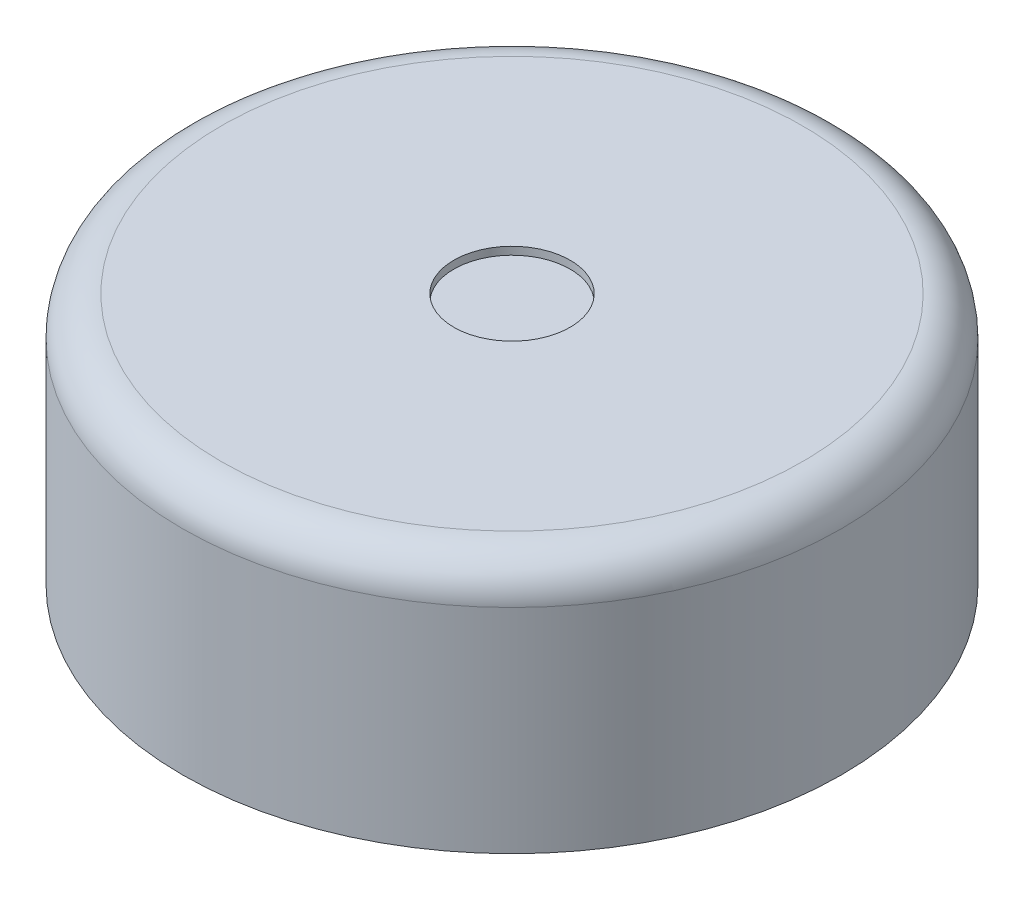
SolidWorks part; units mm, degrees
material "ABS"
ref_plane "Front Plane" through (0, 0, 0) normal (0, 0, 1) x (1, 0, 0)
ref_plane "Top Plane" through (0, 0, 0) normal (0, 1, 0) x (1, 0, 0)
ref_plane "Right Plane" through (0, 0, 0) normal (1, 0, 0) x (0, 0, -1)
sketch "Sketch1" plane through (0, 0, 0) normal (0, 1, 0) x (1, 0, 0)
  circle A0 centre (0, 0) radius 8.5
  dimension "D1" = 17
extrude "Boss-Extrude1" add sketch "Sketch1" along normal blind 7.8
sketch "Sketch2" plane through (0, 7.8, 0) normal (0, 1, 0) x (1, 0, 0)
  circle A1 centre (0, 0) radius 8.5
  circle A2 centre (0, 0) radius 8.5
  circle A3 centre (0, 0) radius 1.5
  circle A4 centre (0, 0) radius 7.8
  circle A5 centre (0, 0) radius 7.8
  circle M3 centre (0, 0) radius 8.5
  dimension "D3" = 3
  dimension "D1" = 0
  dimension "D2" = 0.7
extrude "Cut-Extrude1" cut sketch "Sketch2" against normal blind 1.5 contours A3 | A5 M3
sketch "Sketch3" plane through (0, 0, 0) normal (0, -1, 0) x (1, 0, 0)
  line L0 (-5, 5) -> (5, -5) construction
  circle A0 centre (-5, 5) radius 0.5
  circle A1 centre (5, -5) radius 0.5
  point P4 (0, 0)
  dimension "D1" = 1
  dimension "D2" = 10
  dimension "D3" = 10
extrude "Boss-Extrude2" add sketch "Sketch3" along normal blind 2
chamfer "Chamfer1" distance 0.5 distance2 0.1 2 edges at (-5, -2, 4.5) (5, -2, -5.5)
fillet "Fillet1" radius 1 2 edges at (-5, -1.5, 4.5) (5, -1.5, -5.5)
sketch "Sketch4" plane through (0, 7.8, 0) normal (0, 1, 0) x (1, 0, 0)
  circle A1 centre (0, 0) radius 7.8
  circle A2 centre (0, 0) radius 7.8
  dimension "D1" = 0
extrude "Cut-Extrude2" cut sketch "Sketch4" against normal blind 1.3
sketch "Sketch5" plane through (0, 6.3, 0) normal (0, 1, 0) x (1, 0, 0)
  circle A0 centre (0, 0) radius 7.8 construction
  circle A1 centre (0, 0) radius 8.5
  circle A2 centre (0, 0) radius 8.5
  circle A3 centre (0, 0) radius 7.8
  dimension "D1" = 0
extrude "Boss-Extrude3" add sketch "Sketch5" along normal up to surface (0.2 mm away) up to face at (0, 6.5, 7.8)
fillet "Fillet2" radius 1 1 edges at (0, 6.5, 8.5)
